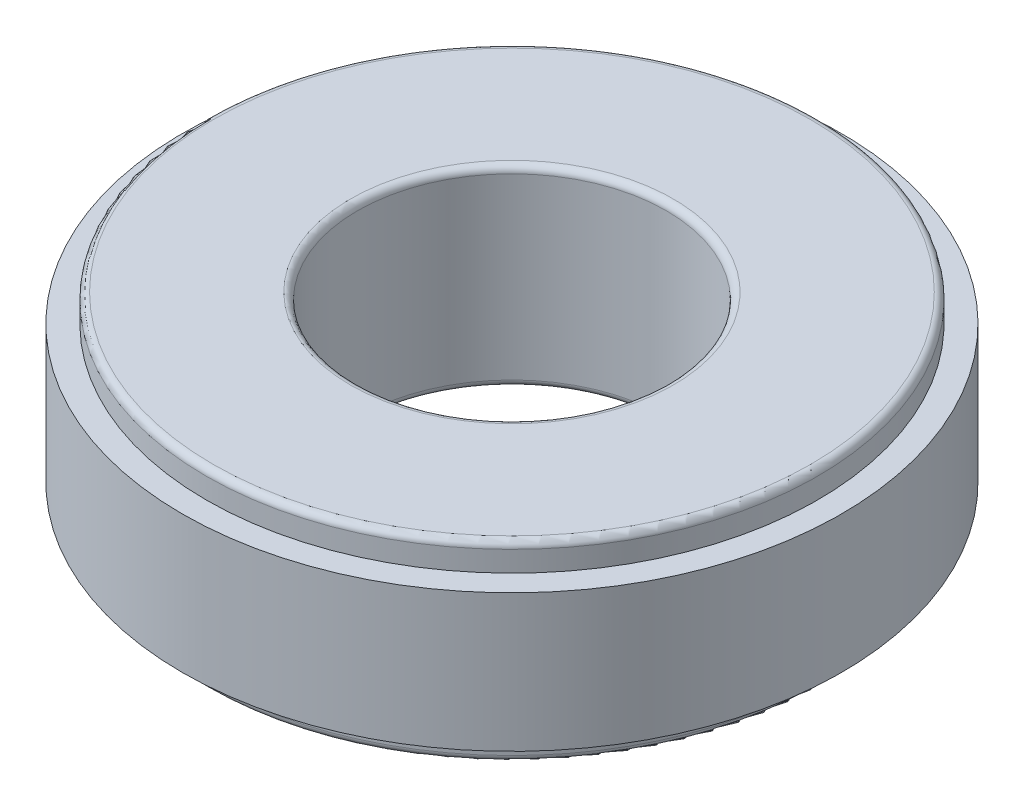
SolidWorks part; units mm, degrees
ref_plane "Front" through (0, 0, 0) normal (0, 0, 1) x (1, 0, 0)
ref_plane "Top" through (0, 0, 0) normal (0, 1, 0) x (1, 0, 0)
ref_plane "Right" through (0, 0, 0) normal (1, 0, 0) x (0, 0, -1)
sketch "Sketch1" plane through (0, 0, 0) normal (0, 1, 0) x (1, 0, 0)
  circle A0 centre (0, 0) radius 28.2575
  dimension "D1" = 56.515
extrude "Step" add sketch "Sketch1" along normal blind 2.54
sketch "Sketch2" plane through (0, 2.54, 0) normal (0, 1, 0) x (1, 0, 0)
  circle A0 centre (0, 0) radius 30.48
  dimension "D1" = 60.96
extrude "Body" add sketch "Sketch2" along normal blind 12.7
sketch "Sketch3" plane through (0, 15.24, 0) normal (0, 1, 0) x (1, 0, 0)
  circle A0 centre (0, 0) radius 28.2575
  dimension "D1" = 56.515
extrude "Boss-Extrude3" add sketch "Sketch3" along normal blind 2.54
sketch "Sketch4" plane through (0, 17.78, 0) normal (0, 1, 0) x (1, 0, 0)
  circle A0 centre (0, 0) radius 14.2875
  dimension "D1" = 28.575
extrude "Cut-Extrude1" cut sketch "Sketch4" against normal through all
fillet "Fillet1" radius 0.635 4 edges at (0, 17.78, 28.2575) (0, 0, 28.2575) (0, 0, 14.2875) (0, 17.78, 14.2875)
